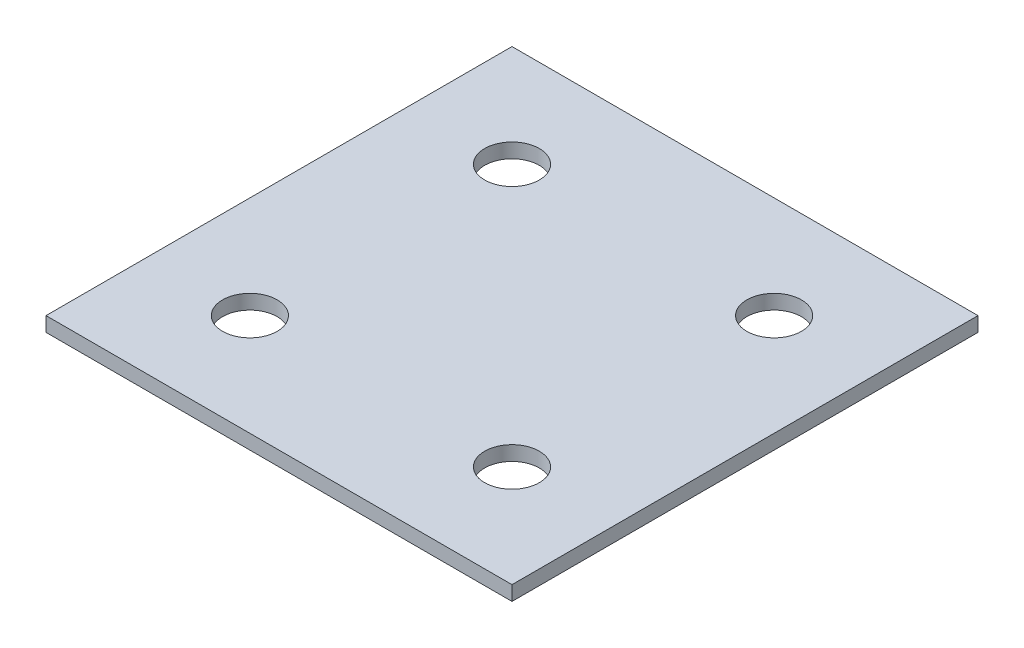
SolidWorks part; units mm, degrees
material "ASTM A36 Steel"
ref_plane "Front Plane" through (0, 0, 0) normal (0, 0, 1) x (1, 0, 0)
ref_plane "Top Plane" through (0, 0, 0) normal (0, 1, 0) x (1, 0, 0)
ref_plane "Right Plane" through (0, 0, 0) normal (1, 0, 0) x (0, 0, -1)
sketch "Sketch2" plane through (0, 0, 0) normal (0, 1, 0) x (1, 0, 0)
  line L1 (0, 0) -> (203.2, 0)
  line L2 (0, 0) -> (0, 203.2)
  line L3 (0, 203.2) -> (203.2, 203.2)
  line L4 (203.2, 0) -> (203.2, 203.2)
  circle A0 centre (44.45, 158.75) radius 11.9062
  circle A1 centre (44.45, 44.45) radius 11.9062
  circle A2 centre (158.75, 158.75) radius 11.9062
  circle A3 centre (158.75, 44.45) radius 11.9062
  dimension "D6" = 23.8125
  dimension "D7" = 44.45
  dimension "D1" = 203.2
  dimension "D2" = 203.2
  dimension "D3" = 44.45
  dimension "D4" = 44.45
  dimension "D5" = 44.45
extrude "Boss-Extrude1" add sketch "Sketch2" along normal blind 6.35
